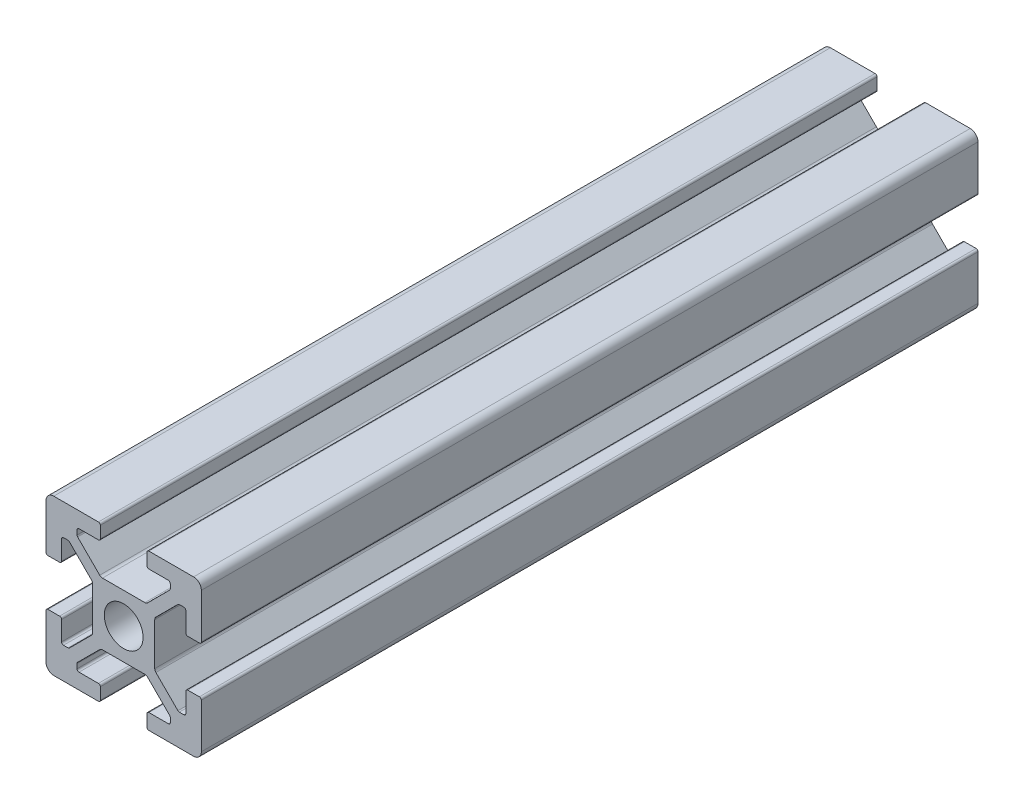
SolidWorks part; units mm, degrees
ref_plane "Front Plane" through (0, 0, 0) normal (0, 0, 1) x (1, 0, 0)
ref_plane "Top Plane" through (0, 0, 0) normal (0, 1, 0) x (1, 0, 0)
ref_plane "Right Plane" through (0, 0, 0) normal (1, 0, 0) x (0, 0, -1)
sketch "Sketch2" plane through (0, 0, 0) normal (0, 0, 1) x (1, 0, 0)
  line L0 (10, 3.25) -> (10, 9)
  line L1 (9, 10) -> (3.25, 10)
  line L2 (3, 9.75) -> (3, 8.25)
  line L3 (3.25, 8) -> (5.75, 8)
  line L4 (6, 7.75) -> (6, 7.1642)
  line L5 (5.9268, 6.9874) -> (3.0858, 4.1464)
  line L6 (2.7322, 4) -> (-2.7322, 4)
  line L7 (-3.0858, 4.1464) -> (-5.9268, 6.9874)
  line L8 (-6, 7.1642) -> (-6, 7.75)
  line L9 (-5.75, 8) -> (-3.25, 8)
  line L10 (-3, 8.25) -> (-3, 9.75)
  line L11 (-3.25, 10) -> (-9, 10)
  line L12 (-10, 9) -> (-10, 3.25)
  line L13 (-9.75, 3) -> (-8.25, 3)
  line L14 (-8, 3.25) -> (-8, 5.75)
  line L15 (-7.75, 6) -> (-7.1642, 6)
  line L16 (-6.9874, 5.9268) -> (-4.1464, 3.0858)
  line L17 (-4, 2.7322) -> (-4, -2.7322)
  line L18 (-4.1464, -3.0858) -> (-6.9874, -5.9268)
  line L19 (-7.1642, -6) -> (-7.75, -6)
  line L20 (-8, -5.75) -> (-8, -3.25)
  line L21 (-8.25, -3) -> (-9.75, -3)
  line L22 (-10, -3.25) -> (-10, -9)
  line L23 (-9, -10) -> (-3.25, -10)
  line L24 (-3, -9.75) -> (-3, -8.25)
  line L25 (-3.25, -8) -> (-5.75, -8)
  line L26 (-6, -7.75) -> (-6, -7.1642)
  line L27 (-5.9268, -6.9874) -> (-3.0858, -4.1464)
  line L28 (-2.7322, -4) -> (2.7322, -4)
  line L29 (3.0858, -4.1464) -> (5.9268, -6.9874)
  line L30 (6, -7.1642) -> (6, -7.75)
  line L31 (5.75, -8) -> (3.25, -8)
  line L32 (3, -8.25) -> (3, -9.75)
  line L33 (3.25, -10) -> (9, -10)
  line L34 (10, -9) -> (10, -3.25)
  line L35 (9.75, -3) -> (8.25, -3)
  line L36 (8, -3.25) -> (8, -5.75)
  line L37 (7.75, -6) -> (7.1642, -6)
  line L38 (6.9874, -5.9268) -> (4.1464, -3.0858)
  line L39 (4, -2.7322) -> (4, 2.7322)
  line L40 (4.1464, 3.0858) -> (6.9874, 5.9268)
  line L41 (7.1642, 6) -> (7.75, 6)
  line L42 (8, 5.75) -> (8, 3.25)
  line L43 (8.25, 3) -> (9.75, 3)
  circle A0 centre (0, 0) radius 2.5
  arc A1 (9.75, 3) -> (10, 3.25) centre (9.75, 3.25) ccw
  arc A2 (10, 9) -> (9, 10) centre (9, 9) ccw
  arc A3 (3.25, 10) -> (3, 9.75) centre (3.25, 9.75) ccw
  arc A4 (3, 8.25) -> (3.25, 8) centre (3.25, 8.25) ccw
  arc A5 (6, 7.75) -> (5.75, 8) centre (5.75, 7.75) ccw
  arc A6 (5.9268, 6.9874) -> (6, 7.1642) centre (5.75, 7.1642) ccw
  arc A7 (2.7322, 4) -> (3.0858, 4.1464) centre (2.7322, 4.5) ccw
  arc A8 (-3.0858, 4.1464) -> (-2.7322, 4) centre (-2.7322, 4.5) ccw
  arc A9 (-6, 7.1642) -> (-5.9268, 6.9874) centre (-5.75, 7.1642) ccw
  arc A10 (-5.75, 8) -> (-6, 7.75) centre (-5.75, 7.75) ccw
  arc A11 (-3.25, 8) -> (-3, 8.25) centre (-3.25, 8.25) ccw
  arc A12 (-3, 9.75) -> (-3.25, 10) centre (-3.25, 9.75) ccw
  arc A13 (-9, 10) -> (-10, 9) centre (-9, 9) ccw
  arc A14 (-10, 3.25) -> (-9.75, 3) centre (-9.75, 3.25) ccw
  arc A15 (-8.25, 3) -> (-8, 3.25) centre (-8.25, 3.25) ccw
  arc A16 (-7.75, 6) -> (-8, 5.75) centre (-7.75, 5.75) ccw
  arc A17 (-6.9874, 5.9268) -> (-7.1642, 6) centre (-7.1642, 5.75) ccw
  arc A18 (-4, 2.7322) -> (-4.1464, 3.0858) centre (-4.5, 2.7322) ccw
  arc A19 (-4.1464, -3.0858) -> (-4, -2.7322) centre (-4.5, -2.7322) ccw
  arc A20 (-7.1642, -6) -> (-6.9874, -5.9268) centre (-7.1642, -5.75) ccw
  arc A21 (-8, -5.75) -> (-7.75, -6) centre (-7.75, -5.75) ccw
  arc A22 (-8, -3.25) -> (-8.25, -3) centre (-8.25, -3.25) ccw
  arc A23 (-9.75, -3) -> (-10, -3.25) centre (-9.75, -3.25) ccw
  arc A24 (-10, -9) -> (-9, -10) centre (-9, -9) ccw
  arc A25 (-3.25, -10) -> (-3, -9.75) centre (-3.25, -9.75) ccw
  arc A26 (-3, -8.25) -> (-3.25, -8) centre (-3.25, -8.25) ccw
  arc A27 (-6, -7.75) -> (-5.75, -8) centre (-5.75, -7.75) ccw
  arc A28 (-5.9268, -6.9874) -> (-6, -7.1642) centre (-5.75, -7.1642) ccw
  arc A29 (-2.7322, -4) -> (-3.0858, -4.1464) centre (-2.7322, -4.5) ccw
  arc A30 (3.0858, -4.1464) -> (2.7322, -4) centre (2.7322, -4.5) ccw
  arc A31 (6, -7.1642) -> (5.9268, -6.9874) centre (5.75, -7.1642) ccw
  arc A32 (5.75, -8) -> (6, -7.75) centre (5.75, -7.75) ccw
  arc A33 (3.25, -8) -> (3, -8.25) centre (3.25, -8.25) ccw
  arc A34 (3, -9.75) -> (3.25, -10) centre (3.25, -9.75) ccw
  arc A35 (9, -10) -> (10, -9) centre (9, -9) ccw
  arc A36 (10, -3.25) -> (9.75, -3) centre (9.75, -3.25) ccw
  arc A37 (8.25, -3) -> (8, -3.25) centre (8.25, -3.25) ccw
  arc A38 (7.75, -6) -> (8, -5.75) centre (7.75, -5.75) ccw
  arc A39 (6.9874, -5.9268) -> (7.1642, -6) centre (7.1642, -5.75) ccw
  arc A40 (4, -2.7322) -> (4.1464, -3.0858) centre (4.5, -2.7322) ccw
  arc A41 (4.1464, 3.0858) -> (4, 2.7322) centre (4.5, 2.7322) ccw
  arc A42 (7.1642, 6) -> (6.9874, 5.9268) centre (7.1642, 5.75) ccw
  arc A43 (8, 5.75) -> (7.75, 6) centre (7.75, 5.75) ccw
  arc A44 (8, 3.25) -> (8.25, 3) centre (8.25, 3.25) ccw
extrude "Boss-Extrude1" add sketch "Sketch2" along normal blind 100
